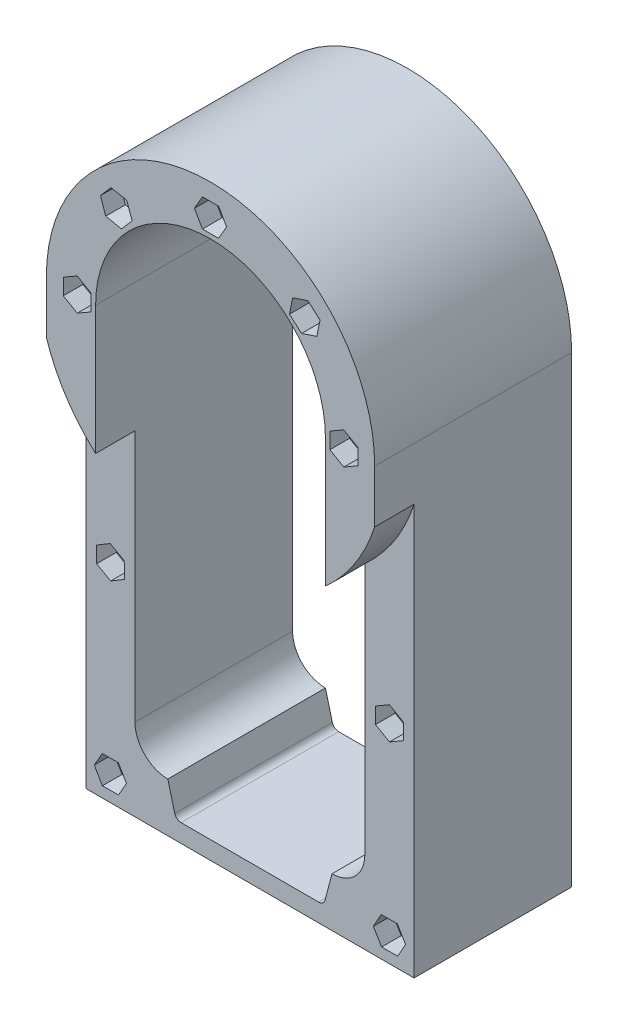
SolidWorks part; units mm, degrees
ref_plane "Alzado" through (0, 0, 0) normal (0, 0, 1) x (1, 0, 0)
ref_plane "Planta" through (0, 0, 0) normal (0, 1, 0) x (1, 0, 0)
ref_plane "Vista lateral" through (0, 0, 0) normal (1, 0, 0) x (0, 0, -1)
sketch "Croquis1" plane through (0, 0, 0) normal (0, 0, 1) x (1, 0, 0)
  line L0 (-35, 0) -> (-35, -116)
  line L1 (-25, -126) -> (25, -126)
  line L2 (35, 0) -> (35, -116)
  line L3 (-50, 0) -> (-50, -141)
  line L4 (-50, -141) -> (50, -141)
  line L5 (50, 0) -> (50, -141)
  line L6 (35, 0) -> (35, -126) construction
  line L7 (-35, -126) -> (35, -126) construction
  line L8 (-35, 0) -> (-35, -126) construction
  arc A0 (35, 0) -> (-35, 0) centre (0, 0) ccw
  arc A1 (50, 0) -> (-50, 0) centre (0, 0) ccw
  arc A2 (35, -116) -> (25, -126) centre (25, -116) cw
  arc A3 (-35, -116) -> (-25, -126) centre (-25, -116) ccw
  dimension "D1" = 141
  dimension "D2" = 15
  dimension "D3" = 10
extrude "Saliente-Extruir1" add sketch "Croquis1" along normal blind 60
sketch "Croquis2" plane through (0, 0, 60) normal (0, 0, 1) x (1, 0, 0)
  circle A0 centre (0, 0) radius 40.605
  circle A1 centre (0, 40.605) radius 3
  circle A2 centre (28.7121, 28.7121) radius 3
  circle A3 centre (40.605, 0) radius 3
  circle A4 centre (28.7121, -28.7121) radius 3
  circle A5 centre (0, -40.605) radius 3
  circle A6 centre (-28.7121, -28.7121) radius 3
  circle A7 centre (-40.605, 0) radius 3
  circle A8 centre (-28.7121, 28.7121) radius 3
  point P22 (0, 0)
  dimension "D1" = 81.21
  dimension "D2" = 6
  dimension "D3" = 8
extrude "Cortar-Extruir1" cut sketch "Croquis2" against normal blind 60 contours A8 | A7 | A1 | A2 | A3
sketch "Croquis3" plane through (0, 0, 60) normal (0, 0, 1) x (1, 0, 0)
  line L1 (4.9075, 40.605) -> (2.4537, 44.855)
  line L2 (2.4537, 44.855) -> (-2.4537, 44.855)
  line L3 (-2.4537, 44.855) -> (-4.9075, 40.605)
  line L4 (-4.9075, 40.605) -> (-2.4537, 36.355)
  line L5 (-2.4537, 36.355) -> (2.4537, 36.355)
  line L6 (2.4537, 36.355) -> (4.9075, 40.605)
  line L7 (33.3651, 30.2717) -> (29.688, 33.5215)
  line L8 (29.688, 33.5215) -> (25.0349, 31.9619)
  line L9 (25.0349, 31.9619) -> (24.059, 27.1525)
  line L10 (24.059, 27.1525) -> (27.7362, 23.9026)
  line L11 (27.7362, 23.9026) -> (32.3893, 25.4622)
  line L12 (32.3893, 25.4622) -> (33.3651, 30.2717)
  line L13 (40.605, -4.9075) -> (44.855, -2.4537)
  line L14 (44.855, -2.4537) -> (44.855, 2.4537)
  line L15 (44.855, 2.4537) -> (40.605, 4.9075)
  line L16 (40.605, 4.9075) -> (36.355, 2.4537)
  line L17 (36.355, 2.4537) -> (36.355, -2.4537)
  line L18 (36.355, -2.4537) -> (40.605, -4.9075)
  line L19 (-33.5289, 29.6508) -> (-31.9335, 25.0099)
  line L20 (-31.9335, 25.0099) -> (-27.1166, 24.0712)
  line L21 (-27.1166, 24.0712) -> (-23.8952, 27.7733)
  line L22 (-23.8952, 27.7733) -> (-25.4907, 32.4142)
  line L23 (-25.4907, 32.4142) -> (-30.3075, 33.353)
  line L24 (-30.3075, 33.353) -> (-33.5289, 29.6508)
  line L25 (-40.605, 4.9075) -> (-44.855, 2.4537)
  line L26 (-44.855, 2.4537) -> (-44.855, -2.4537)
  line L27 (-44.855, -2.4537) -> (-40.605, -4.9075)
  line L28 (-40.605, -4.9075) -> (-36.355, -2.4537)
  line L29 (-36.355, -2.4537) -> (-36.355, 2.4537)
  line L30 (-36.355, 2.4537) -> (-40.605, 4.9075)
  circle A0 centre (0, 40.605) radius 4.25 construction
  circle A1 centre (28.7121, 28.7121) radius 4.25 construction
  circle A2 centre (40.605, 0) radius 4.25 construction
  circle A3 centre (-28.7121, 28.7121) radius 4.25 construction
  circle A4 centre (-40.605, 0) radius 4.25 construction
  dimension "D1" = 8.5
  dimension "D2" = 8.5
  dimension "D3" = 8.5
  dimension "D4" = 8.5
  dimension "D5" = 8.5
extrude "Cortar-Extruir2" cut sketch "Croquis3" against normal blind 6
sketch "Croquis4" plane through (0, 0, 60) normal (0, 0, 1) x (1, 0, 0)
  line L0 (-50, -16.0078) -> (-50, -141)
  line L1 (-50, -141) -> (50, -141)
  line L2 (50, -141) -> (50, -16.0078)
  arc A0 (-50, -16.0078) -> (50, -16.0078) centre (0, 0) ccw
  dimension "D1" = 105
extrude "Cortar-Extruir3" cut sketch "Croquis4" against normal blind 12
sketch "Croquis5" plane through (0, 0, 48) normal (0, 0, 1) x (1, 0, 0)
  line L0 (-35, -77.5656) -> (-50, -77.5656) construction
  line L1 (-35, -39.1312) -> (-35, -116) construction
  line L2 (-50, -16.0078) -> (-50, -141) construction
  line L3 (0, -141) -> (0, -126) construction
  line L4 (-50, -141) -> (50, -141) construction
  line L5 (-25, -126) -> (25, -126) construction
  line L6 (0, -133.5) -> (-50, -133.5) construction
  line L7 (-42.5, -77.5656) -> (-42.5, -133.5) construction
  line L8 (42.5, -77.5656) -> (42.5, -133.5) construction
  circle A0 centre (-42.5, -77.5656) radius 3
  circle A1 centre (-42.5, -133.5) radius 3
  circle A2 centre (42.5, -77.5656) radius 3
  circle A3 centre (42.5, -133.5) radius 3
  dimension "D1" = 6
extrude "Cortar-Extruir4" cut sketch "Croquis5" against normal up to surface (48 mm away) up to face at (43.605, 0, 0)
sketch "Croquis6" plane through (0, 0, 48) normal (0, 0, 1) x (1, 0, 0)
  line L1 (-42.4213, -82.4724) -> (-38.2112, -79.9509)
  line L2 (-38.2112, -79.9509) -> (-38.2899, -75.044)
  line L3 (-38.2899, -75.044) -> (-42.5787, -72.6587)
  line L4 (-42.5787, -72.6587) -> (-46.7888, -75.1803)
  line L5 (-46.7888, -75.1803) -> (-46.7101, -80.0872)
  line L6 (-46.7101, -80.0872) -> (-42.4213, -82.4724)
  line L7 (42.5, -82.4731) -> (46.75, -80.0193)
  line L8 (46.75, -80.0193) -> (46.75, -75.1119)
  line L9 (46.75, -75.1119) -> (42.5, -72.6581)
  line L10 (42.5, -72.6581) -> (38.25, -75.1119)
  line L11 (38.25, -75.1119) -> (38.25, -80.0193)
  line L12 (38.25, -80.0193) -> (42.5, -82.4731)
  line L13 (-40.0636, -129.2401) -> (-44.971, -129.26)
  line L14 (-44.971, -129.26) -> (-47.4074, -133.52)
  line L15 (-47.4074, -133.52) -> (-44.9364, -137.7599)
  line L16 (-44.9364, -137.7599) -> (-40.029, -137.74)
  line L17 (-40.029, -137.74) -> (-37.5926, -133.48)
  line L18 (-37.5926, -133.48) -> (-40.0636, -129.2401)
  line L19 (44.896, -129.2172) -> (39.9889, -129.2836)
  line L20 (39.9889, -129.2836) -> (37.593, -133.5664)
  line L21 (37.593, -133.5664) -> (40.104, -137.7828)
  line L22 (40.104, -137.7828) -> (45.0111, -137.7164)
  line L23 (45.0111, -137.7164) -> (47.407, -133.4336)
  line L24 (47.407, -133.4336) -> (44.896, -129.2172)
  circle A0 centre (-42.5, -77.5656) radius 4.25 construction
  circle A1 centre (42.5, -77.5656) radius 4.25 construction
  circle A2 centre (-42.5, -133.5) radius 4.25 construction
  circle A3 centre (42.5, -133.5) radius 4.25 construction
  dimension "D1" = 8.5
extrude "Cortar-Extruir5" cut sketch "Croquis6" against normal blind 6
sketch "Croquis7" plane through (0, 0, 0) normal (0, 0, -1) x (-1, 0, 0)
  line L1 (2.3579, 44.9089) -> (-2.5484, 44.7989)
  line L2 (-2.5484, 44.7989) -> (-4.9062, 40.495)
  line L3 (-4.9062, 40.495) -> (-2.3579, 36.3011)
  line L4 (-2.3579, 36.3011) -> (2.5484, 36.4111)
  line L5 (2.5484, 36.4111) -> (4.9062, 40.715)
  line L6 (4.9062, 40.715) -> (2.3579, 44.9089)
  line L7 (-40.6144, 4.9075) -> (-44.8597, 2.4456)
  line L8 (-44.8597, 2.4456) -> (-44.8503, -2.4619)
  line L9 (-44.8503, -2.4619) -> (-40.5956, -4.9075)
  line L10 (-40.5956, -4.9075) -> (-36.3503, -2.4456)
  line L11 (-36.3503, -2.4456) -> (-36.3597, 2.4619)
  line L12 (-36.3597, 2.4619) -> (-40.6144, 4.9075)
  line L13 (44.8825, -2.4055) -> (44.827, 2.5017)
  line L14 (44.827, 2.5017) -> (40.5495, 4.9072)
  line L15 (40.5495, 4.9072) -> (36.3275, 2.4055)
  line L16 (36.3275, 2.4055) -> (36.383, -2.5017)
  line L17 (36.383, -2.5017) -> (40.6605, -4.9072)
  line L18 (40.6605, -4.9072) -> (44.8825, -2.4055)
  line L19 (-42.1314, -72.672) -> (-46.5537, -74.7995)
  line L20 (-46.5537, -74.7995) -> (-46.9223, -79.6932)
  line L21 (-46.9223, -79.6932) -> (-42.8686, -82.4592)
  line L22 (-42.8686, -82.4592) -> (-38.4463, -80.3316)
  line L23 (-38.4463, -80.3316) -> (-38.0777, -75.438)
  line L24 (-38.0777, -75.438) -> (-42.1314, -72.672)
  line L25 (42.0844, -72.6757) -> (38.0575, -75.4806)
  line L26 (38.0575, -75.4806) -> (38.4731, -80.3705)
  line L27 (38.4731, -80.3705) -> (42.9156, -82.4554)
  line L28 (42.9156, -82.4554) -> (46.9425, -79.6506)
  line L29 (46.9425, -79.6506) -> (46.5269, -74.7607)
  line L30 (46.5269, -74.7607) -> (42.0844, -72.6757)
  line L31 (47.4075, -133.5) -> (44.9537, -129.25)
  line L32 (44.9537, -129.25) -> (40.0463, -129.25)
  line L33 (40.0463, -129.25) -> (37.5925, -133.5)
  line L34 (37.5925, -133.5) -> (40.0463, -137.75)
  line L35 (40.0463, -137.75) -> (44.9537, -137.75)
  line L36 (44.9537, -137.75) -> (47.4075, -133.5)
  line L37 (-44.6369, -137.9178) -> (-39.7425, -137.5595)
  line L38 (-39.7425, -137.5595) -> (-37.6056, -133.1417)
  line L39 (-37.6056, -133.1417) -> (-40.3631, -129.0822)
  line L40 (-40.3631, -129.0822) -> (-45.2575, -129.4405)
  line L41 (-45.2575, -129.4405) -> (-47.3944, -133.8583)
  line L42 (-47.3944, -133.8583) -> (-44.6369, -137.9178)
  circle A0 centre (0, 40.605) radius 4.25 construction
  circle A1 centre (-40.605, 0) radius 4.25 construction
  circle A2 centre (40.605, 0) radius 4.25 construction
  circle A3 centre (-42.5, -77.5656) radius 4.25 construction
  circle A4 centre (42.5, -77.5656) radius 4.25 construction
  circle A5 centre (42.5, -133.5) radius 4.25 construction
  circle A6 centre (-42.5, -133.5) radius 4.25 construction
  dimension "D1" = 8.5
  dimension "D2" = 8.5
extrude "Cortar-Extruir6" cut sketch "Croquis7" against normal blind 6
sketch "Croquis8" plane through (0, 0, 48) normal (0, 0, 1) x (1, 0, 0)
  line L0 (0, -141) -> (0, -113) construction
  line L2 (-50, -141) -> (50, -141) construction
  line L3 (0, 0) -> (0, -113) construction
  line L4 (-22.8924, -134.009) -> (-25, -126)
  line L13 (-20.9582, -135.5) -> (20.9582, -135.5)
  line L17 (-25, -126) -> (25, -126)
  line L18 (25, -126) -> (22.8924, -134.009)
  arc A0 (22.8924, -134.009) -> (20.9582, -135.5) centre (20.9582, -133.5) cw
  arc A1 (-22.8924, -134.009) -> (-20.9582, -135.5) centre (-20.9582, -133.5) ccw
  dimension "D2" = 2
  dimension "D1" = 28
extrude "Cortar-Extruir7" cut sketch "Croquis8" against normal up to surface (48 mm away) up to face at (42.5, -133.5, 0)
